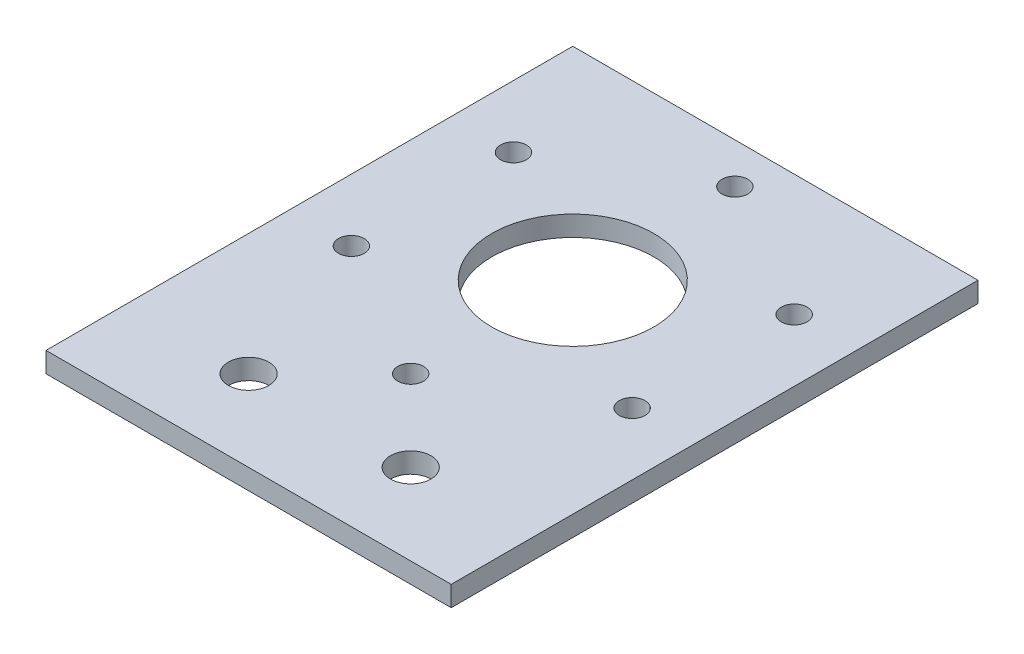
SolidWorks part; units mm, degrees
ref_plane "Front Plane" through (0, 0, 0) normal (0, 0, 1) x (1, 0, 0)
ref_plane "Top Plane" through (0, 0, 0) normal (0, 1, 0) x (1, 0, 0)
ref_plane "Right Plane" through (0, 0, 0) normal (1, 0, 0) x (0, 0, -1)
sketch "Sketch1" plane through (0, 0, 0) normal (0, 1, 0) x (1, 0, 0)
  line L0 (31.75, 0) -> (31.75, 50.8) construction
  line L1 (0, 0) -> (63.5, 0)
  line L2 (0, 0) -> (0, 82.55)
  line L3 (0, 82.55) -> (63.5, 82.55)
  line L4 (63.5, 0) -> (63.5, 82.55)
  line L6 (31.75, 76.2) -> (9.753, 63.5) construction
  line L7 (9.753, 63.5) -> (9.753, 38.1) construction
  line L8 (9.753, 38.1) -> (31.75, 25.4) construction
  line L9 (31.75, 25.4) -> (53.747, 38.1) construction
  line L10 (53.747, 38.1) -> (53.747, 63.5) construction
  line L11 (53.747, 63.5) -> (31.75, 76.2) construction
  circle A0 centre (31.75, 50.8) radius 12.7
  circle A1 centre (31.75, 50.8) radius 25.4 construction
  circle A2 centre (31.75, 50.8) radius 21.997 construction
  circle A3 centre (9.753, 63.5) radius 2.0193
  circle A4 centre (31.75, 76.2) radius 2.0193
  circle A5 centre (53.747, 63.5) radius 2.0193
  circle A6 centre (53.747, 38.1) radius 2.0193
  circle A7 centre (31.75, 25.4) radius 2.0193
  circle A8 centre (9.753, 38.1) radius 2.0193
  dimension "D4" = 25.4
  dimension "D5" = 50.8
  dimension "D6" = 4.0386
  dimension "D1" = 82.55
  dimension "D2" = 63.5
  dimension "D3" = 50.8
extrude "Boss-Extrude1" add sketch "Sketch1" along normal blind 3.175
sketch "Sketch2" plane through (0, 3.175, 0) normal (0, 1, 0) x (1, 0, 0)
  line L0 (0, 12.7) -> (19.05, 12.7) construction
  line L1 (0, 82.55) -> (0, 0) construction
  line L2 (19.05, 12.7) -> (44.45, 12.7) construction
  line L3 (44.45, 12.7) -> (63.5, 12.7) construction
  line L4 (63.5, 0) -> (63.5, 82.55) construction
  line L5 (0, 0) -> (63.5, 0) construction
  circle A0 centre (19.05, 12.7) radius 3.175
  circle A1 centre (44.45, 12.7) radius 3.175
  dimension "D3" = 6.35
  dimension "D1" = 25.4
  dimension "D2" = 12.7
extrude "Cut-Extrude1" cut sketch "Sketch2" against normal through all
